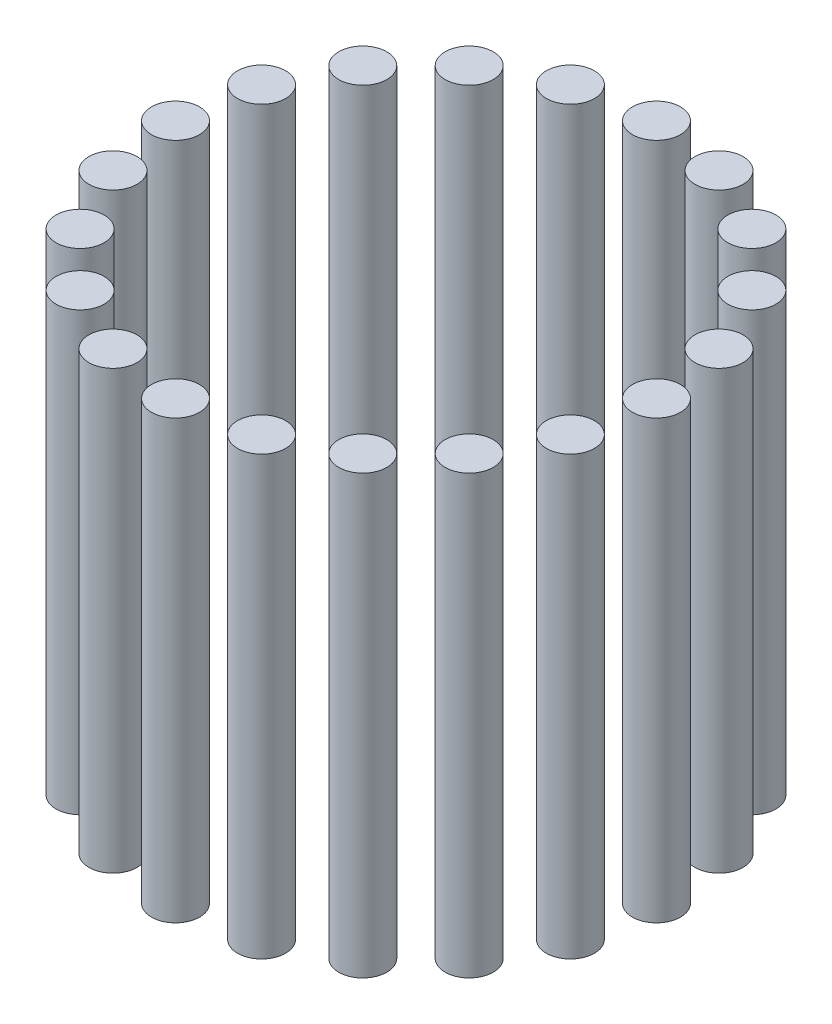
SolidWorks part; units mm, degrees
ref_plane "Front Plane" through (0, 0, 0) normal (0, 0, 1) x (1, 0, 0)
ref_plane "Top Plane" through (0, 0, 0) normal (0, 1, 0) x (1, 0, 0)
ref_plane "Right Plane" through (0, 0, 0) normal (1, 0, 0) x (0, 0, -1)
sketch "Sketch1" plane through (0, 0, 0) normal (0, 1, 0) x (1, 0, 0)
  circle A1 centre (55, 0) radius 5.5
  circle A2 centre (52.3081, -16.9959) radius 5.5
  circle A3 centre (44.4959, -32.3282) radius 5.5
  circle A4 centre (32.3282, -44.4959) radius 5.5
  circle A5 centre (16.9959, -52.3081) radius 5.5
  circle A6 centre (0, -55) radius 5.5
  circle A7 centre (-16.9959, -52.3081) radius 5.5
  circle A8 centre (-32.3282, -44.4959) radius 5.5
  circle A9 centre (-44.4959, -32.3282) radius 5.5
  circle A10 centre (-52.3081, -16.9959) radius 5.5
  circle A11 centre (-55, 0) radius 5.5
  circle A12 centre (-52.3081, 16.9959) radius 5.5
  circle A13 centre (-44.4959, 32.3282) radius 5.5
  circle A14 centre (-32.3282, 44.4959) radius 5.5
  circle A15 centre (-16.9959, 52.3081) radius 5.5
  circle A16 centre (0, 55) radius 5.5
  circle A17 centre (16.9959, 52.3081) radius 5.5
  circle A18 centre (32.3282, 44.4959) radius 5.5
  circle A19 centre (44.4959, 32.3282) radius 5.5
  circle A20 centre (52.3081, 16.9959) radius 5.5
  point P46 (0, 0)
  dimension "D1" = 20
extrude "Boss-Extrude1" add sketch "Sketch1" along normal blind 100
